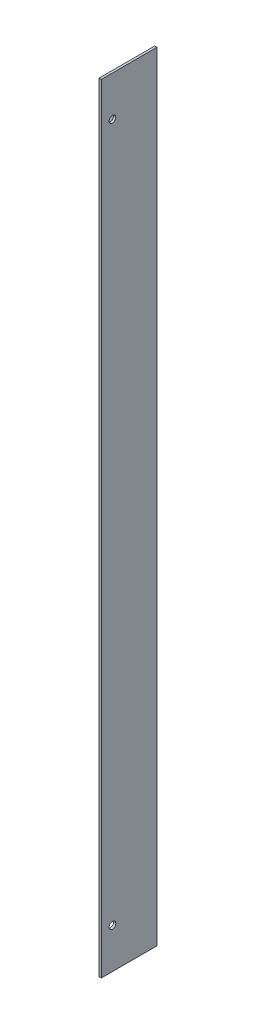
SolidWorks part; units mm, degrees
material "Plástico personalizado"
ref_plane "Alzado" through (0, 0, 0) normal (0, 0, 1) x (1, 0, 0)
ref_plane "Planta" through (0, 0, 0) normal (0, 1, 0) x (1, 0, 0)
ref_plane "Vista lateral" through (0, 0, 0) normal (1, 0, 0) x (0, 0, -1)
sketch "Croquis1" plane through (0, 0, 0) normal (0, 0, 1) x (1, 0, 0)
  line L0 (-55.4418, 61.1804) -> (-79.4418, 37.1804)
  line L1 (-79.4418, -264.8196) -> (-79.4418, 37.1804)
  line L4 (-55.4418, 61.1804) -> (-55.4418, -288.8196)
  line L5 (-55.4418, -288.8196) -> (-79.4418, -264.8196)
  circle A0 centre (-74.4418, 21.1804) radius 1.5
  circle A1 centre (-74.4418, -248.8196) radius 1.5
  circle A2 centre (-74.4418, -168.8196) radius 1.5
  dimension "D1" = 5
  dimension "D4" = 24
  dimension "D9" = 5
  dimension "D2" = 350
  dimension "D3" = 5
  dimension "D5" = 40
  dimension "D6" = 40
  dimension "D7" = 45
  dimension "D8" = 45
  dimension "D10" = 120
sketch "Croquis2" plane through (0, 0, 0) normal (0, 0, 1) x (1, 0, 0)
  line L1 (-55.4418, 61.1804) -> (-54.4418, 61.1804)
  line L2 (-55.4418, 61.1804) -> (-55.4418, -288.8196)
  line L3 (-55.4418, -288.8196) -> (-54.4418, -288.8196)
  line L4 (-54.4418, 61.1804) -> (-54.4418, -288.8196)
  dimension "D1" = 1
  dimension "D2" = 350
extrude "Saliente-Extruir2" add sketch "Croquis2" along normal blind 25
sketch "Croquis5" plane through (-54.4418, 0, 0) normal (1, 0, 0) x (0, 0, -1)
  line L0 (-25, 61.1804) -> (0, 61.1804) construction
  line L1 (-25, -288.8196) -> (0, -288.8196) construction
  line L2 (-25, -288.8196) -> (-25, 61.1804) construction
  circle A0 centre (-20, 43.1804) radius 1.5
  circle A1 centre (-20, -270.8196) radius 1.5
  dimension "D1" = 18
  dimension "D4" = 5
  dimension "D2" = 18
  dimension "D3" = 5
extrude "Cortar-Extruir2" cut sketch "Croquis5" against normal blind 1
extrude "Saliente-Extruir3" add sketch "Croquis1" along normal blind 1
